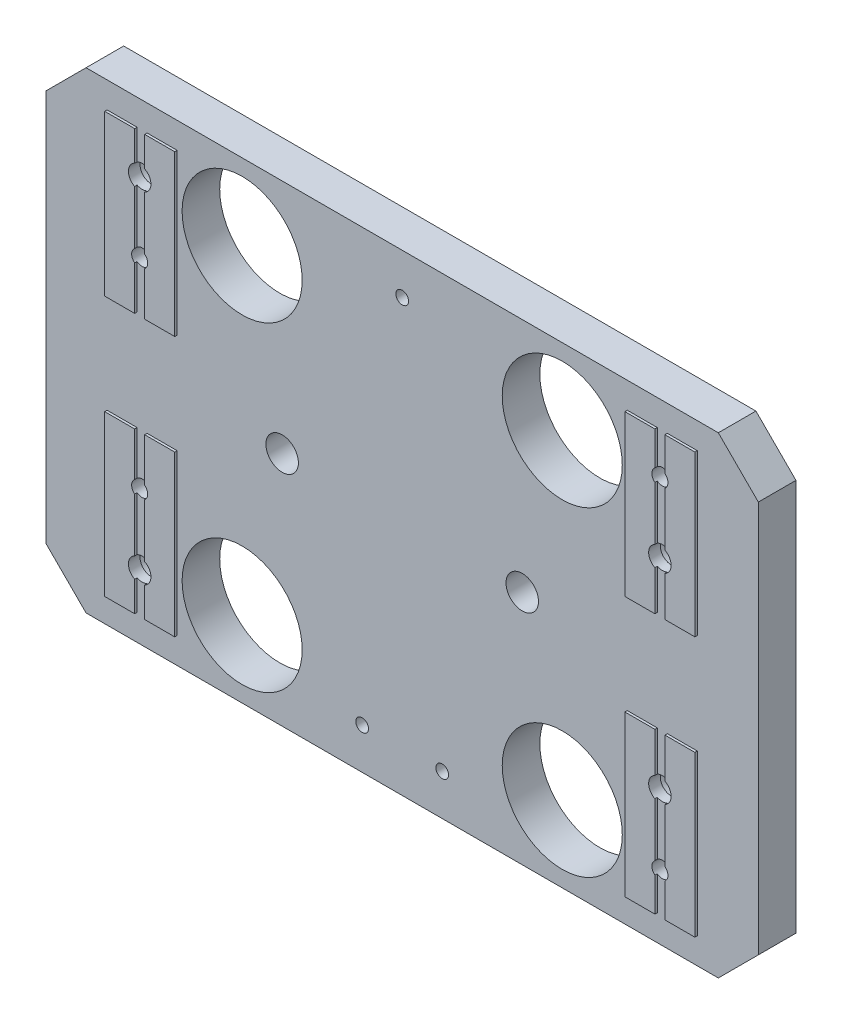
SolidWorks part; units mm, degrees
material "6061-T6 Al"
ref_plane "Front" through (0, 0, 0) normal (0, 0, 1) x (1, 0, 0)
ref_plane "Top" through (0, 0, 0) normal (0, 1, 0) x (1, 0, 0)
ref_plane "Right" through (0, 0, 0) normal (1, 0, 0) x (0, 0, -1)
sketch "Sketch3" plane through (0, 0, 0) normal (0, 0, 1) x (1, 0, 0)
  line L1 (0, 0) -> (226.06, 0)
  line L2 (0, 0) -> (0, -149.86)
  line L3 (0, -149.86) -> (226.06, -149.86)
  line L4 (226.06, 0) -> (226.06, -149.86)
  dimension "D1" = 226.06
  dimension "D2" = 149.86
extrude "Extrude2" add sketch "Sketch3" along normal blind 12.7
sketch "Sketch4" plane through (0, 0, 12.7) normal (0, 0, 1) x (1, 0, 0)
  line L0 (0, -74.93) -> (226.06, -74.93) construction
  line L1 (0, 0) -> (0, -149.86) construction
  line L2 (226.06, -149.86) -> (226.06, 0) construction
  line L3 (113.03, 0) -> (113.03, -149.86) construction
  line L4 (226.06, 0) -> (0, 0) construction
  line L5 (0, -149.86) -> (226.06, -149.86) construction
  line L7 (41.6052, -8.255) -> (41.6052, -59.055)
  line L8 (19.3802, -8.255) -> (19.3802, -59.055)
  line L10 (41.6052, -141.605) -> (41.6052, -90.805)
  line L11 (19.3802, -141.605) -> (19.3802, -90.805)
  line L13 (184.4548, -141.605) -> (184.4548, -90.805)
  line L14 (206.6798, -141.605) -> (206.6798, -90.805)
  line L16 (184.4548, -8.255) -> (184.4548, -59.055)
  line L17 (206.6798, -8.255) -> (206.6798, -59.055)
  line L18 (206.6798, -141.605) -> (184.4548, -141.605)
  line L19 (0, 0) -> (226.06, 0)
  line L20 (0, 0) -> (0, -149.86)
  line L21 (0, -149.86) -> (226.06, -149.86)
  line L22 (226.06, 0) -> (226.06, -149.86)
  line L23 (206.6798, -90.805) -> (184.4548, -90.805)
  line L24 (206.6798, -59.055) -> (184.4548, -59.055)
  line L25 (206.6798, -8.255) -> (184.4548, -8.255)
  line L26 (41.6052, -141.605) -> (19.3802, -141.605)
  line L27 (41.6052, -90.805) -> (19.3802, -90.805)
  line L28 (41.6052, -59.055) -> (19.3802, -59.055)
  line L29 (41.6052, -8.255) -> (19.3802, -8.255)
  dimension "D1" = 15.875
  dimension "D2" = 15.875
  dimension "D3" = 50.8
  dimension "D4" = 50.8
  dimension "D5" = 71.4248
  dimension "D6" = 71.4248
  dimension "D7" = 22.225
  dimension "D8" = 22.225
extrude "Extrude4" cut sketch "Sketch4" against normal blind 0.762
hole_wizard "CBORE for 1/4 Socket Head Cap Screw1" positions "3DSketch4" profile "Sketch9" counterbore size "1/4" standard "Ansi Inch" end condition through all
sketch3d "3DSketch4"
  line L1 (226.06, -74.93, 0) -> (0, -74.93, 0) construction
  line L2 (226.06, -149.86, 0) -> (226.06, 0, 0) construction
  line L3 (0, 0, 0) -> (0, -149.86, 0) construction
  line L5 (113.03, 0, 0) -> (113.03, -149.86, 0) construction
  line L6 (226.06, 0, 0) -> (0, 0, 0) construction
  line L7 (0, -149.86, 0) -> (226.06, -149.86, 0) construction
  line L10 (195.58, -43.18, 0) -> (195.58, -74.93, 0) construction
  line L12 (195.58, -74.93, 0) -> (195.58, -106.68, 0) construction
  line L14 (30.48, -20.955, 0) -> (30.48, -74.93, 0) construction
  line L16 (30.48, -74.93, 0) -> (30.48, -128.905, 0) construction
  point P4 (195.58, -106.68, 0)
  point P6 (30.48, -20.955, 0)
  point P8 (30.48, -128.905, 0)
  point P10 (195.58, -43.18, 0)
  dimension "D1" = 82.55
  dimension "D2" = 63.5
  dimension "D3" = 107.95
  dimension "D4" = 82.55
sketch "Sketch9" plane through (195.58, -106.68, 0) normal (1, 0, 0) x (0, 1, 0)
  line L0 (0, 0) -> (0, 12.7)
  line L1 (0, 12.7) -> (3.5712, 12.7)
  line L3 (3.5712, 12.7) -> (3.5712, 9.017)
  line L4 (5.5562, 9.017) -> (3.5712, 9.017)
  line L5 (5.5562, 9.017) -> (5.5562, 0.635)
  line L6 (5.5562, 0.635) -> (6.1913, 0)
  line L7 (6.1913, 0) -> (0, 0)
  line L8 (-5.5562, 0.635) -> (-6.1913, 0) construction
  line L11 (0, -6.35) -> (0, 107.95) construction
  dimension "Thru Hole Dia." = 7.1425
  dimension "Thru Hole Depth" = 12.7
  dimension "C'Bore Dia." = 11.1125
  dimension "C'Bore Depth" = 9.017
  dimension "Near C'Sink Dia." = 12.3825
  dimension "Near C'Sink Angle" = 90
hole_wizard "1 (1) Diameter Hole1" positions "3DSketch6" profile "Sketch14" hole size "1" standard "Ansi Inch" end condition through all
sketch3d "3DSketch6"
  line L0 (113.03, 0, 0) -> (113.03, -149.86, 0) construction
  line L1 (226.06, 0, 0) -> (0, 0, 0) construction
  line L2 (0, -149.86, 0) -> (226.06, -149.86, 0) construction
  line L4 (0, -74.93, 0) -> (226.06, -74.93, 0) construction
  line L5 (0, 0, 0) -> (0, -149.86, 0) construction
  line L6 (226.06, -149.86, 0) -> (226.06, 0, 0) construction
  line L7 (163.83, -24.13, 0) -> (163.83, -74.93, 0) construction
  line L9 (163.83, -74.93, 0) -> (163.83, -125.73, 0) construction
  line L17 (163.83, -24.13, 0) -> (113.03, -24.13, 0) construction
  line L20 (113.03, -24.13, 0) -> (62.23, -24.13, 0) construction
  point P0 (163.83, -24.13, 0)
  point P2 (62.23, -24.13, 0)
  point P4 (62.23, -125.73, 0)
  point P6 (163.83, -125.73, 0)
  dimension "D1" = 101.6
  dimension "D2" = 101.6
sketch "Sketch14" plane through (163.83, -24.13, 0) normal (1, 0, 0) x (0, 1, 0)
  line L0 (0, 0) -> (0, 12.7)
  line L1 (0, 12.7) -> (19.05, 12.7)
  line L2 (19.05, 12.7) -> (19.05, 0)
  line L5 (19.05, 0) -> (0, 0)
  line L11 (0, -6.35) -> (0, 107.95) construction
  dimension "Thru Hole Dia." = 38.1
  dimension "Thru Hole Depth" = 12.7
hole_wizard "#10-32 Tapped Hole1" positions "Sketch18" profile "Sketch17" tap size "#10-32" standard "Ansi Inch" end condition through all
sketch "Sketch18" plane through (0, 0, 0) normal (0, 0, -1) x (-1, 0, 0)
  line L10 (-113.03, 0) -> (-113.03, -149.86) construction
  line L11 (-226.06, 0) -> (0, 0) construction
  line L12 (0, -149.86) -> (-226.06, -149.86) construction
  line L13 (0, -74.93) -> (-226.06, -74.93) construction
  line L14 (0, 0) -> (0, -149.86) construction
  line L15 (-226.06, -149.86) -> (-226.06, 0) construction
  line L16 (-113.03, -13.0048) -> (-113.03, -74.93) construction
  line L17 (-125.73, -136.8552) -> (-100.33, -136.8552) construction
  point P0 (-125.73, -136.8552)
  point P1 (-113.03, -13.0048)
  point P54 (-100.33, -136.8552)
  dimension "D1" = 61.9252
  dimension "D2" = 25.4
  dimension "D3" = 12.7
  dimension "D4" = 61.9252
sketch "Sketch17" plane through (125.73, -136.8552, 0) normal (1, 0, 0) x (0, 1, 0)
  line L0 (0, 0) -> (0, 12.7)
  line L1 (0, 12.7) -> (2.0193, 12.7)
  line L2 (2.0193, 12.7) -> (2.0193, 0)
  line L5 (2.0193, 0) -> (0, 0)
  line L11 (0, -6.35) -> (0, 107.95) construction
  dimension "Thru Tap Drill Dia." = 4.0386
  dimension "Thru Tap Drill Depth" = 12.7
cosmetic thread "Hole Thread1" parameters "D2"=4.826
cosmetic thread "Hole Thread2" parameters "D2"=4.826
cosmetic thread "Hole Thread7" parameters "D2"=4.826
sketch "Sketch19" plane through (0, 0, 12.7) normal (0, 0, 1) x (1, 0, 0)
  line L0 (195.58, -106.68) -> (195.58, -141.605) construction
  line L1 (197.1675, -141.605) -> (193.9925, -141.605)
  line L2 (197.1675, -141.605) -> (197.1675, -8.255)
  line L3 (197.1675, -8.255) -> (193.9925, -8.255)
  line L4 (193.9925, -141.605) -> (193.9925, -8.255)
  line L5 (32.0675, -141.605) -> (28.8925, -141.605)
  line L6 (32.0675, -141.605) -> (32.0675, -8.255)
  line L7 (32.0675, -8.255) -> (28.8925, -8.255)
  line L8 (28.8925, -141.605) -> (28.8925, -8.255)
  line L9 (30.48, -128.905) -> (30.48, -141.605) construction
  line L10 (184.4548, -141.605) -> (206.6798, -141.605) construction
  line L11 (19.3802, -141.605) -> (41.6052, -141.605) construction
  line L12 (41.6052, -8.255) -> (19.3802, -8.255) construction
  line L13 (206.6798, -8.255) -> (184.4548, -8.255) construction
  dimension "D1" = 3.175
extrude "Cut-Extrude1" cut sketch "Sketch19" against normal up to surface (0.762 mm away) up to face at (127.7493, -136.8552, 11.938)
hole_wizard "1/4-20 Tapped Hole1" positions "Sketch21" profile "Sketch20" tap size "1/4-20" standard "Ansi Inch" end condition through all
sketch "Sketch21" plane through (0, 0, 0) normal (0, 0, -1) x (-1, 0, 0)
  line L0 (-30.48, -20.955) -> (-195.58, -20.955) construction
  line L1 (-195.58, -20.955) -> (-195.58, -43.18) construction
  line L2 (-195.58, -43.18) -> (-195.58, -106.68) construction
  line L3 (-195.58, -106.68) -> (-195.58, -128.905) construction
  line L4 (-30.48, -20.955) -> (-30.48, -43.18) construction
  line L5 (-195.58, -43.18) -> (-30.48, -43.18) construction
  line L6 (-30.48, -43.18) -> (-30.48, -106.68) construction
  line L7 (-195.58, -106.68) -> (-30.48, -106.68) construction
  line L8 (-30.48, -128.905) -> (-195.58, -128.905) construction
  point P0 (-195.58, -128.905)
  point P1 (-195.58, -20.955)
  point P4 (-30.48, -43.18)
  point P6 (-30.48, -106.68)
sketch "Sketch20" plane through (195.58, -128.905, 0) normal (1, 0, 0) x (0, 1, 0)
  line L0 (0, 0) -> (0, 12.7)
  line L1 (0, 12.7) -> (2.5527, 12.7)
  line L2 (2.5527, 12.7) -> (2.5527, 0)
  line L5 (2.5527, 0) -> (0, 0)
  line L11 (0, -6.35) -> (0, 107.95) construction
  dimension "Thru Tap Drill Dia." = 5.1054
  dimension "Thru Tap Drill Depth" = 12.7
cosmetic thread "Hole Thread3" parameters "D1"=11.1252, "D2"=6.35
cosmetic thread "Hole Thread4" parameters "D1"=11.1252, "D2"=6.35
cosmetic thread "Hole Thread5" parameters "D1"=11.1252, "D2"=6.35
cosmetic thread "Hole Thread6" parameters "D1"=11.1252, "D2"=6.35
chamfer "Chamfer1" distance 12.7 angle 45 4 edges at (226.06, -149.86, 5.969) (226.06, 0, 5.969) (0, -149.86, 5.969) (0, 0, 5.969)
hole_wizard "13/32 (0.40625) Diameter Hole1" positions "Sketch24" profile "Sketch23" hole size "13/32" standard "Ansi Inch" end condition through all
sketch "Sketch24" plane through (0, 0, 0) normal (0, 0, -1) x (-1, 0, 0)
  line L2 (-74.93, -74.93) -> (0, -74.93) construction
  line L3 (0, -12.7) -> (0, -137.16) construction
  line L4 (-113.03, 0) -> (-113.03, -149.86) construction
  line L5 (-213.36, 0) -> (-12.7, 0) construction
  line L6 (-12.7, -149.86) -> (-213.36, -149.86) construction
  line L7 (-74.93, -74.93) -> (-113.03, -74.93) construction
  line L8 (-151.13, -74.93) -> (-113.03, -74.93) construction
  point P0 (-74.93, -74.93)
  point P11 (-151.13, -74.93)
  dimension "D1" = 38.1
sketch "Sketch23" plane through (74.93, -74.93, 0) normal (1, 0, 0) x (0, 1, 0)
  line L0 (0, 0) -> (0, 12.7)
  line L1 (0, 12.7) -> (5.1594, 12.7)
  line L2 (5.1594, 12.7) -> (5.1594, 0)
  line L5 (5.1594, 0) -> (0, 0)
  line L11 (0, -6.35) -> (0, 107.95) construction
  dimension "Thru Hole Dia." = 10.3187
  dimension "Thru Hole Depth" = 12.7
